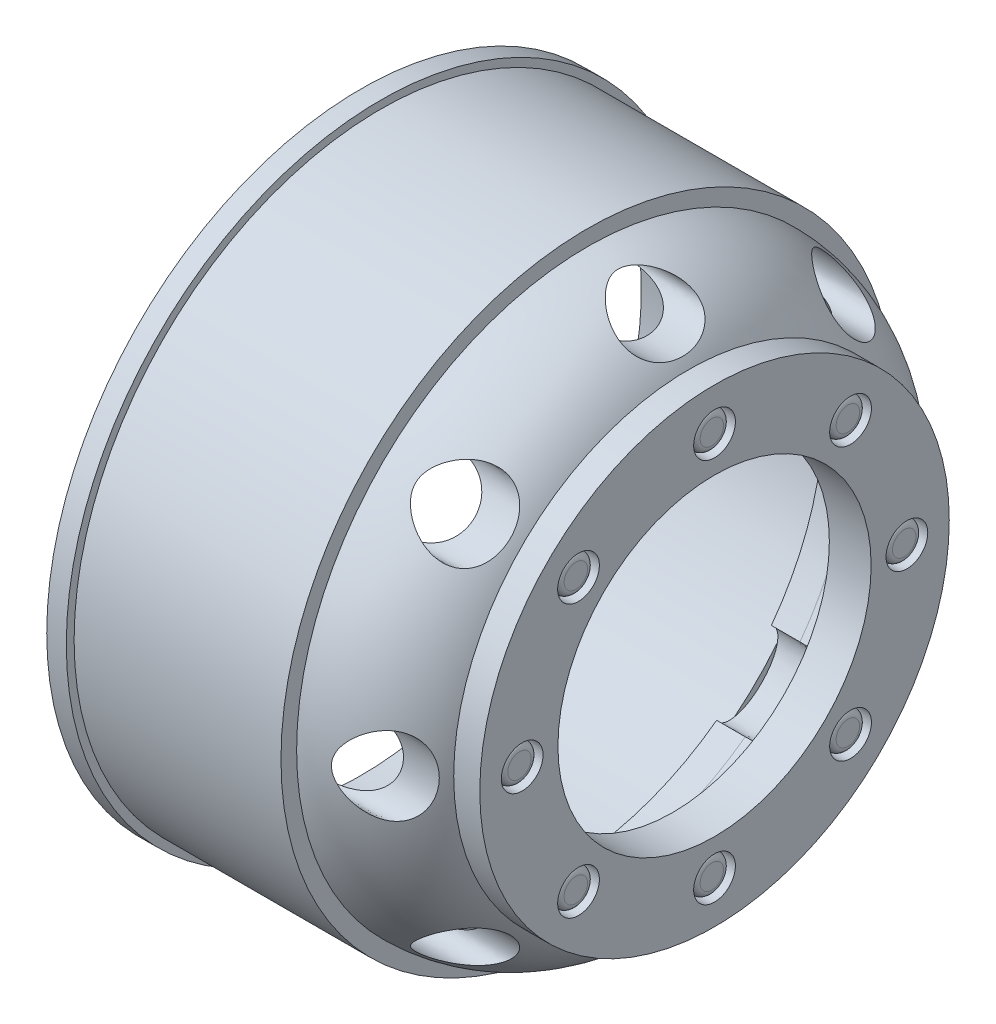
SolidWorks part; units mm, degrees
ref_plane "Front Plane" through (0, 0, 0) normal (0, 0, 1) x (1, 0, 0)
ref_plane "Top Plane" through (0, 0, 0) normal (0, 1, 0) x (1, 0, 0)
ref_plane "Right Plane" through (0, 0, 0) normal (1, 0, 0) x (0, 0, -1)
sketch "Sketch1" plane through (0, 0, 0) normal (0, 0, 1) x (1, 0, 0)
  line L0 (-25, 0) -> (25, 0) construction
  line L1 (0, 36.6286) -> (0, -30.4082) construction
  line L2 (-9.8613, 23.5) -> (6, 23.5)
  line L36 (13.7458, 18) -> (15.7458, 18)
  line L43 (-9.8613, 21.5) -> (3.8066, 21.5)
  line L44 (6, 20.3) -> (3.8066, 20.3)
  line L45 (3.8066, 20.3) -> (3.8066, 21.5)
  line L47 (12.542, 16) -> (12.542, 8.4837)
  line L48 (-9.8613, 21.5) -> (11.1, 21.5) construction
  line L49 (15.7458, 18) -> (15.7458, 0) construction
  line L51 (13.7458, 16) -> (13.7458, 0) construction
  line L52 (12.542, 8.4837) -> (15.7458, 8.4837)
  line L53 (15.7458, 8.4837) -> (15.7458, 18)
  line L54 (6, 22.3) -> (6, 23.5)
  line L55 (12.542, 16) -> (13.7458, 16) construction
  line L56 (-9.8613, 23.5) -> (-9.8613, 24.1)
  line L57 (-9.8613, 23.5) -> (11.1, 23.5) construction
  line L58 (-9.8613, 24.1) -> (-11.3613, 24.1)
  line L59 (-11.3613, 24.1) -> (-11.3613, 21.5)
  line L60 (-11.3613, 21.5) -> (-10.2717, 21.5)
  line L61 (-10.2717, 21.5) -> (-9.8613, 21.5)
  arc A4 (6, 22.3) -> (13.7458, 18) centre (6, 13.1735) cw
  arc A5 (6, 20.3) -> (12.542, 16) centre (6, 13.1735) cw
  point P13 (12.9671, 14)
  point P21 (16.5518, 14)
  point P24 (12.9671, 11)
  point P27 (16.5518, 11)
  dimension "D1" = 50
  dimension "D2" = 25
  dimension "D3" = 2
  dimension "D4" = 1.5
  dimension "D5" = 0.6
  dimension "D9" = 2
  dimension "D10" = 2
  dimension "D11" = 47
revolve "Revolve1" add sketch "Sketch1" angle 360 about L0
sketch "Sketch3" plane through (15.7458, 0, 0) normal (1, 0, 0) x (0, 0, -1)
  line L0 (0, 22.3) -> (0, -22.3) construction
  line L1 (-22.3, 0) -> (22.3, 0) construction
  circle A2 centre (0, 0) radius 22.3 construction
  ellipse E0 centre (0, 20.3231) end of major axis (3, 20.3231) minor radius 1.6667
  dimension "D1" = 6
sketch "Sketch5" plane through (15.7458, 0, 0) normal (1, 0, 0) x (0, 0, -1)
  circle A0 centre (0, 0) radius 14.75 construction
  circle A1 centre (0, 14.75) radius 1.6
  circle A2 centre (10.4298, 10.4298) radius 1.6
  circle A3 centre (14.75, 0) radius 1.6
  circle A4 centre (10.4298, -10.4298) radius 1.6
  circle A5 centre (0, -14.75) radius 1.6
  circle A6 centre (-10.4298, -10.4298) radius 1.6
  circle A7 centre (-14.75, 0) radius 1.6
  circle A8 centre (-10.4298, 10.4298) radius 1.6
  point P22 (0, 0)
  dimension "D1" = 29.5
  dimension "D2" = 3.2
  dimension "D3" = 8
extrude "Cut-Extrude3" cut sketch "Sketch5" against normal offset from surface (1.7038 mm away) 1.5 up to face at (12.542, 0, 8.4837)
sketch "Sketch6" plane through (14.042, 0, 0) normal (1, 0, 0) x (0, 0, -1)
  line L0 (-14.75, 1.6) -> (-14.75, -1.6) construction
  line L1 (-16.35, 0) -> (-13.15, 0) construction
  circle A0 centre (-14.75, 0) radius 1.6 construction
  circle A1 centre (-14.75, 0) radius 1.6 construction
  circle A2 centre (-14.75, 0) radius 1.4
  circle A3 centre (-10.4298, 10.4298) radius 1.4
  circle A4 centre (0, 14.75) radius 1.4
  circle A5 centre (10.4298, 10.4298) radius 1.4
  circle A6 centre (14.75, 0) radius 1.4
  circle A7 centre (10.4298, -10.4298) radius 1.4
  circle A8 centre (0, -14.75) radius 1.4
  circle A9 centre (-10.4298, -10.4298) radius 1.4
  point P28 (0, 0)
  dimension "D1" = 2.8
  dimension "D2" = 8
extrude "Boss-Extrude1" add sketch "Sketch6" along normal blind 1.5
fillet "Fillet1" radius 0.5 8 edges at (15.542, 0, -16.15) (15.542, -10.4298, -11.8298) (15.542, -14.75, -1.4) (15.542, -10.4298, 9.0298) (15.542, 0, 13.35) (15.542, 10.4298, 9.0298) (15.542, 14.75, -1.4) (15.542, 10.4298, -11.8298)
sketch "Sketch7" plane through (15.7458, 0, 0) normal (1, 0, 0) x (0, 0, -1)
  circle A0 centre (0, 0) radius 12.0088
extrude "Cut-Extrude4" cut sketch "Sketch7" against normal through all
extrude "Cut-Extrude5" cut sketch "Sketch3" against normal up to surface (11.9392 mm away) up to face at (3.8066, 0, 20.3)
pattern_circular "CirPattern1" count 8 over 360 about axis through (-25, 0, 0) along (-1, 0, 0) of "Cut-Extrude5"
